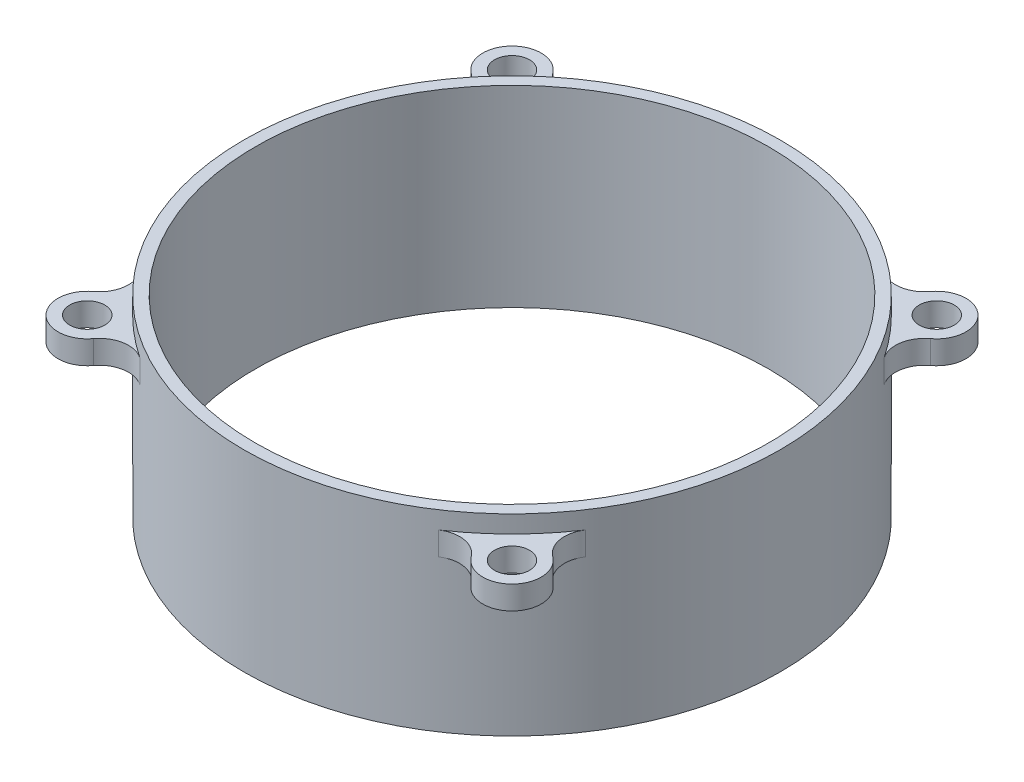
SolidWorks part; units mm, degrees
material "AISI 304"
ref_plane "前视基准面" through (0, 0, 0) normal (0, 0, 1) x (1, 0, 0)
ref_plane "上视基准面" through (0, 0, 0) normal (0, 1, 0) x (1, 0, 0)
ref_plane "右视基准面" through (0, 0, 0) normal (1, 0, 0) x (0, 0, -1)
sketch "草图1" plane through (0, 0, 0) normal (0, 0, 1) x (1, 0, 0)
  line L0 (0, 0) -> (0, 13.2654) construction
  line L1 (22, 1.5) -> (22, -15)
  line L2 (22, -15) -> (23, -15)
  line L5 (23, -15) -> (23, -2)
  line L6 (23, -2) -> (28.25, -2)
  line L7 (28.25, -2) -> (28.25, 0)
  line L8 (28.25, 0) -> (23, 0)
  line L9 (23, 0) -> (23, 1.5)
  line L10 (23, 1.5) -> (22, 1.5)
  dimension "D1" = 56.5
  dimension "D2" = 2
  dimension "D3" = 13
  dimension "D4" = 1.5
  dimension "D5" = 44
  dimension "D6" = 1
revolve "旋转1" add sketch "草图1" angle 360 about L0
sketch "草图2" plane through (0, 0, 0) normal (0, 1, 0) x (1, 0, 0)
  circle A0 centre (0, 0) radius 25.75 construction
  circle A1 centre (-18.208, 18.208) radius 1.5
  circle A2 centre (0, 0) radius 28.25 construction
  circle A3 centre (18.208, 18.208) radius 1.5
  circle A4 centre (18.208, -18.208) radius 1.5
  circle A5 centre (-18.208, -18.208) radius 1.5
  dimension "D1" = 2.5
  dimension "D2" = 3
  dimension "D3" = 4
extrude "切除-拉伸1" cut sketch "草图2" against normal through all
sketch "草图4" plane through (0, 0, 0) normal (0, 1, 0) x (1, 0, 0)
  arc A0 (-16.1998, 19.697) -> (-19.697, 16.1998) centre (-18.208, 18.208) ccw
  arc A1 (-16.1998, 19.697) -> (-12.8003, 19.109) centre (-14.1916, 21.186) ccw
  circle A2 centre (0, 0) radius 23 construction
  arc A3 (-19.697, 16.1998) -> (-19.109, 12.8003) centre (-21.186, 14.1916) cw
  arc A4 (12.8003, 19.109) -> (-12.8003, 19.109) centre (0, 0) ccw
  circle A5 centre (0, 0) radius 28.25 construction
  arc A6 (19.697, 16.1998) -> (16.1998, 19.697) centre (18.208, 18.208) ccw
  arc A7 (19.697, 16.1998) -> (19.109, 12.8003) centre (21.186, 14.1916) ccw
  arc A8 (16.1998, 19.697) -> (12.8003, 19.109) centre (14.1916, 21.186) cw
  arc A9 (19.109, -12.8003) -> (19.109, 12.8003) centre (0, 0) ccw
  arc A10 (16.1998, -19.697) -> (19.697, -16.1998) centre (18.208, -18.208) ccw
  arc A11 (16.1998, -19.697) -> (12.8003, -19.109) centre (14.1916, -21.186) ccw
  arc A12 (19.697, -16.1998) -> (19.109, -12.8003) centre (21.186, -14.1916) cw
  arc A13 (-12.8003, -19.109) -> (12.8003, -19.109) centre (0, 0) ccw
  arc A14 (-19.697, -16.1998) -> (-16.1998, -19.697) centre (-18.208, -18.208) ccw
  arc A15 (-19.697, -16.1998) -> (-19.109, -12.8003) centre (-21.186, -14.1916) ccw
  arc A16 (-16.1998, -19.697) -> (-12.8003, -19.109) centre (-14.1916, -21.186) cw
  arc A17 (-19.109, 12.8003) -> (-19.109, -12.8003) centre (0, 0) ccw
  dimension "D1" = 4
  dimension "D2" = 2.5
extrude "切除-拉伸3" cut sketch "草图4" against normal through all flip side to cut
